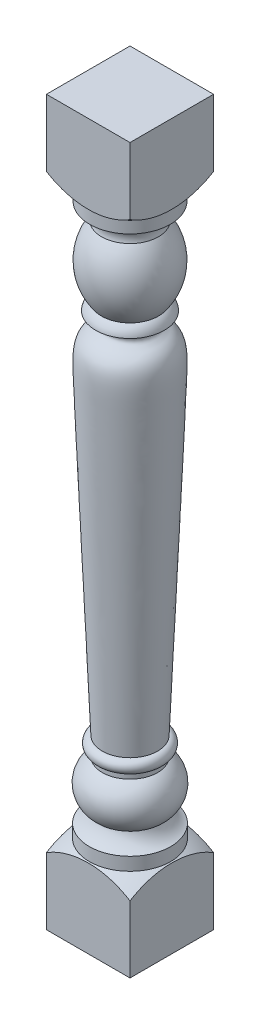
SolidWorks part; units mm, degrees
ref_plane "Front Plane" through (0, 0, 0) normal (0, 0, 1) x (1, 0, 0)
ref_plane "Top Plane" through (0, 0, 0) normal (0, 1, 0) x (1, 0, 0)
ref_plane "Right Plane" through (0, 0, 0) normal (1, 0, 0) x (0, 0, -1)
sketch "Sketch1" plane through (0, 0, 0) normal (0, 0, 1) x (1, 0, 0)
  line L0 (0, 0) -> (0, 965.2) construction
  line L1 (0, -614.68) -> (0, 614.68) construction
  line L2 (0, 965.2) -> (2.54, 965.2) construction
  line L3 (2.54, 965.2) -> (2.54, 942.975) construction
  line L4 (24.13, 130.175) -> (24.13, 120.65) construction
  line L6 (1.905, 0) -> (1.905, 22.225) construction
  arc A0 (2.54, 942.975) -> (22.86, 914.4) centre (-6.6011, 914.9623) cw construction
  arc A1 (22.86, 796.925) -> (22.86, 914.4) centre (97.594, 855.6625) cw construction
  arc A2 (22.86, 796.925) -> (12.7, 781.05) centre (35.8871, 777.399) ccw construction
  arc A3 (24.13, 152.4) -> (24.13, 130.175) centre (25.1271, 141.2875) ccw construction
  arc A4 (1.905, 22.225) -> (22.86, 44.45) centre (-4.0093, 48.7927) ccw construction
  arc A5 (24.13, 120.65) -> (22.86, 44.45) centre (45.3767, 82.1853) ccw construction
  spline S0 degree 3 poles (12.7, 781.05) (20.4619, 780.6915) (49.8326, 761.459) (-1.3952, 733.4357) (9.6428, 585.614) (9.4613, 519.9517) (24.13, 152.4) knots 0 0 0 0 0.151522 0.286773 0.373312 1 1 1 1 construction
  point P5 (2.54, 965.2)
  point P6 (2.54, 942.975)
  point P7 (22.86, 914.4)
  point P12 (2.54, 855.6625)
  point P13 (22.86, 796.925)
  point P14 (12.7, 781.05)
  point P19 (2.54, 714.375)
  point P20 (24.13, 152.4)
  point P22 (24.13, 130.175)
  point P24 (13.97, 141.2875)
  point P28 (24.13, 120.65)
  point P29 (1.524, 79.375)
  point P31 (22.86, 44.45)
  point P32 (1.905, 22.225)
  point P34 (1.905, 0)
  dimension "D1" = 965.2
sketch "Sketch2" plane through (0, 0, 0) normal (0, 0, 1) x (1, 0, 0)
  line L0 (0, -135.6134) -> (0, 0) construction
  line L1 (0, -642.62) -> (0, 642.62) construction
  line L2 (0, -135.6134) -> (71.4375, -135.6134)
  line L3 (71.4375, -135.6134) -> (71.4375, 1101.1371)
  line L4 (71.4375, 1101.1371) -> (0, 1101.1371)
  line L5 (0, 1101.1371) -> (0, 965.2) construction
  line L6 (-80.9625, 1101.1371) -> (0, 1101.1371)
  line L7 (2.54, 965.2) -> (2.54, 942.975)
  line L8 (0, -135.6134) -> (-80.9625, -135.6134)
  line L9 (1.905, 0) -> (1.905, 22.225)
  line L10 (24.13, 120.65) -> (24.13, 130.175)
  arc A0 (1.905, 22.225) -> (22.86, 44.45) centre (-12.3934, 56.6976) ccw
  arc A1 (24.13, 120.65) -> (22.86, 44.45) centre (45.3767, 82.1853) ccw
  arc A2 (24.13, 152.4) -> (24.13, 130.175) centre (25.1271, 141.2875) ccw
  arc A3 (2.54, 942.975) -> (22.86, 914.4) centre (1.9595, 921.0498) cw
  arc A4 (22.86, 914.4) -> (2.54, 942.975) centre (-6.6011, 914.9623) ccw construction
  arc A5 (22.86, 914.4) -> (22.86, 796.925) centre (97.594, 855.6625) ccw
  arc A6 (22.86, 796.925) -> (12.7, 781.05) centre (35.8871, 777.399) ccw
  arc A7 (1.905, 0) -> (-80.9625, -135.6134) centre (71.4375, -135.6134) ccw
  arc A8 (2.54, 965.2) -> (-80.9625, 1101.1371) centre (71.4375, 1101.1371) cw
  spline S0 degree 3 poles (12.7, 781.05) (28.5433, 778.2125) (43.2563, 750.6902) (-0.0352, 758.0128) (6.5863, 584.7537) (4.6831, 626.5173) (24.13, 152.4) knots 0 0 0 0 0.117084 0.342939 0.431231 1 1 1 1
  dimension "D1" = 152.4
  dimension "D3" = 152.4
  dimension "D2" = 71.4375
revolve "Revolve2" add sketch "Sketch2" angle 360 about L3
sketch "Sketch4" plane through (0, 0, 0) normal (0, 1, 0) x (1, 0, 0)
  line L1 (0, 71.4375) -> (142.875, 71.4375)
  line L2 (0, 71.4375) -> (0, -71.4375)
  line L3 (0, -71.4375) -> (142.875, -71.4375)
  line L4 (142.875, 71.4375) -> (142.875, -71.4375)
  point P4 (0, 0)
  dimension "D1" = 142.875
extrude "Cut-Extrude2" cut sketch "Sketch4" against normal through all and the other way through all flip side to cut
scale "Scale1" scale about origin uniform scaling yes scale factor 0.4
